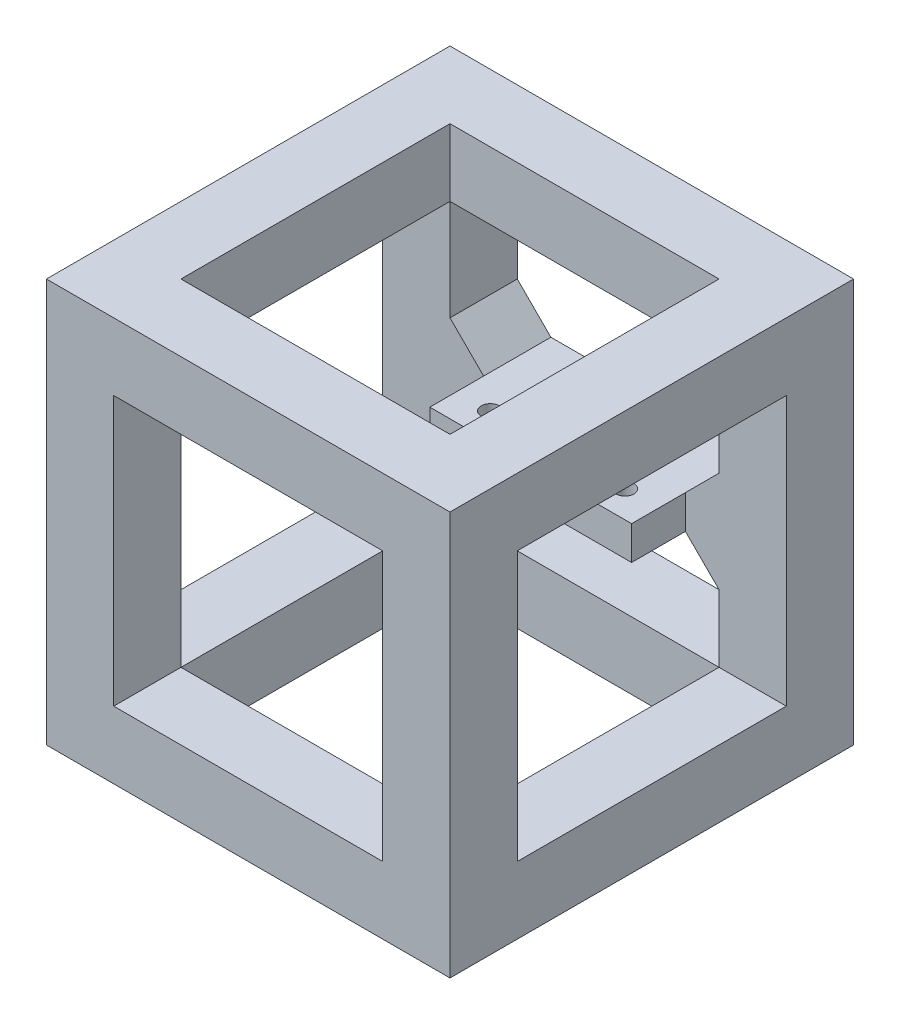
SolidWorks part; units mm, degrees
ref_plane "정면" through (0, 0, 0) normal (0, 0, 1) x (1, 0, 0)
ref_plane "윗면" through (0, 0, 0) normal (0, 1, 0) x (1, 0, 0)
ref_plane "우측면" through (0, 0, 0) normal (1, 0, 0) x (0, 0, -1)
sketch "스케치1" plane through (0, 0, 0) normal (0, 1, 0) x (1, 0, 0)
  line L0 (-10, 0) -> (10, 0) construction
  line L1 (0, 5) -> (0, 0) construction
  line L2 (-15, 14) -> (15, 14)
  line L3 (-15, 14) -> (-15, -4)
  line L4 (-15, -4) -> (15, -4)
  line L5 (15, 14) -> (15, -4)
  line L6 (-15, 14) -> (15, -4) construction
  line L7 (-15, -4) -> (15, 14) construction
  line L8 (-15, 4) -> (15, 4) construction
  circle A0 centre (-10, 0) radius 1.35
  circle A1 centre (10, 0) radius 1.35
  point P3 (0, 5)
  point P4 (0, 0)
  dimension "D1" = 2.7
  dimension "D2" = 2.7
  dimension "D3" = 20
  dimension "D4" = 4
  dimension "D5" = 30
  dimension "D6" = 4
  dimension "D7" = 10
extrude "보스-돌출1" add sketch "스케치1" along normal blind 5
sketch "스케치2" plane through (0, 5, 0) normal (0, 1, 0) x (1, 0, 0)
  line L0 (0, 14) -> (0, -46) construction
  line L1 (15, 14) -> (-15, 14) construction
  line L2 (30, 14) -> (-30, 14)
  line L3 (-30, 14) -> (-30, -46)
  line L4 (-30, -46) -> (30, -46)
  line L5 (20, 4) -> (-20, 4)
  line L6 (-20, 4) -> (-20, -36)
  line L7 (-20, -36) -> (20, -36)
  line L8 (20, 4) -> (20, -36)
  line L9 (30, 14) -> (30, -46)
  point P12 (0, -36)
  point P13 (0, 4)
  dimension "D1" = 10
  dimension "D2" = 10
  dimension "D3" = 10
  dimension "D4" = 30
  dimension "D5" = 60
extrude "보스-돌출2" add sketch "스케치2" along normal blind 30 and the other way blind 30
sketch "스케치3" plane through (0, 0, 46) normal (0, 0, 1) x (1, 0, 0)
  line L0 (-30, 35) -> (30, 35) construction
  line L1 (-20, 25) -> (20, 25)
  line L2 (-20, 25) -> (-20, -15)
  line L3 (-20, -15) -> (20, -15)
  line L4 (20, 25) -> (20, -15)
  line L5 (-20, 25) -> (20, -15) construction
  line L6 (-20, -15) -> (20, 25) construction
  line L7 (30, -25) -> (30, 35) construction
  line L8 (-30, -25) -> (30, -25) construction
  line L9 (-30, -25) -> (-30, 35) construction
  point P0 (0, 5)
  dimension "D1" = 10
  dimension "D2" = 10
  dimension "D3" = 10
  dimension "D4" = 10
extrude "컷-돌출1" cut sketch "스케치3" against normal blind 10
sketch "스케치4" plane through (-30, 0, 0) normal (-1, 0, 0) x (0, 0, 1)
  line L0 (-14, 35) -> (46, 35) construction
  line L1 (-4, 25) -> (36, 25)
  line L2 (-4, 25) -> (-4, -15)
  line L3 (-4, -15) -> (36, -15)
  line L4 (36, 25) -> (36, -15)
  line L5 (-4, 25) -> (36, -15) construction
  line L6 (-4, -15) -> (36, 25) construction
  line L7 (-14, -25) -> (-14, 35) construction
  line L8 (46, -25) -> (46, 35) construction
  line L9 (-14, -25) -> (46, -25) construction
  point P0 (16, 5)
  point P13 (16, -25)
  dimension "D1" = 10
  dimension "D2" = 10
  dimension "D3" = 10
  dimension "D4" = 10
extrude "컷-돌출2" cut sketch "스케치4" against normal blind 10
sketch "스케치5" plane through (30, 0, 0) normal (1, 0, 0) x (0, 0, -1)
  line L0 (-46, 35) -> (14, 35) construction
  line L1 (-46, -25) -> (14, -25) construction
  line L2 (4, -15) -> (-36, -15)
  line L3 (4, -15) -> (4, 25)
  line L4 (4, 25) -> (-36, 25)
  line L5 (-36, -15) -> (-36, 25)
  line L6 (4, -15) -> (-36, 25) construction
  line L7 (4, 25) -> (-36, -15) construction
  line L8 (14, -25) -> (14, 35) construction
  line L9 (-46, -25) -> (-46, 35) construction
  point P1 (-16, 5)
  dimension "D1" = 10
  dimension "D2" = 10
  dimension "D3" = 10
  dimension "D4" = 10
extrude "컷-돌출3" cut sketch "스케치5" against normal blind 10
sketch "스케치6" plane through (0, 0, -4) normal (0, 0, 1) x (1, 0, 0)
  line L0 (20, -15) -> (20, 25) construction
  line L1 (-20, 25) -> (20, 25)
  line L2 (-20, 25) -> (-20, 5)
  line L3 (-20, 5) -> (20, 5)
  line L4 (20, 25) -> (20, 5)
  line L5 (-15, 0) -> (15, 0) construction
  line L6 (20, 0) -> (-20, 0)
  line L7 (20, 0) -> (20, -15)
  line L8 (20, -15) -> (-20, -15)
  line L9 (-20, 0) -> (-20, -15)
  line L10 (-15, 5) -> (15, 5) construction
extrude "컷-돌출4" cut sketch "스케치6" against normal blind 10
chamfer "모따기1" distance 5 angle 45 4 edges at (20, 5, -9) (-20, 5, -9) (-20, 0, -9) (20, 0, -9)
